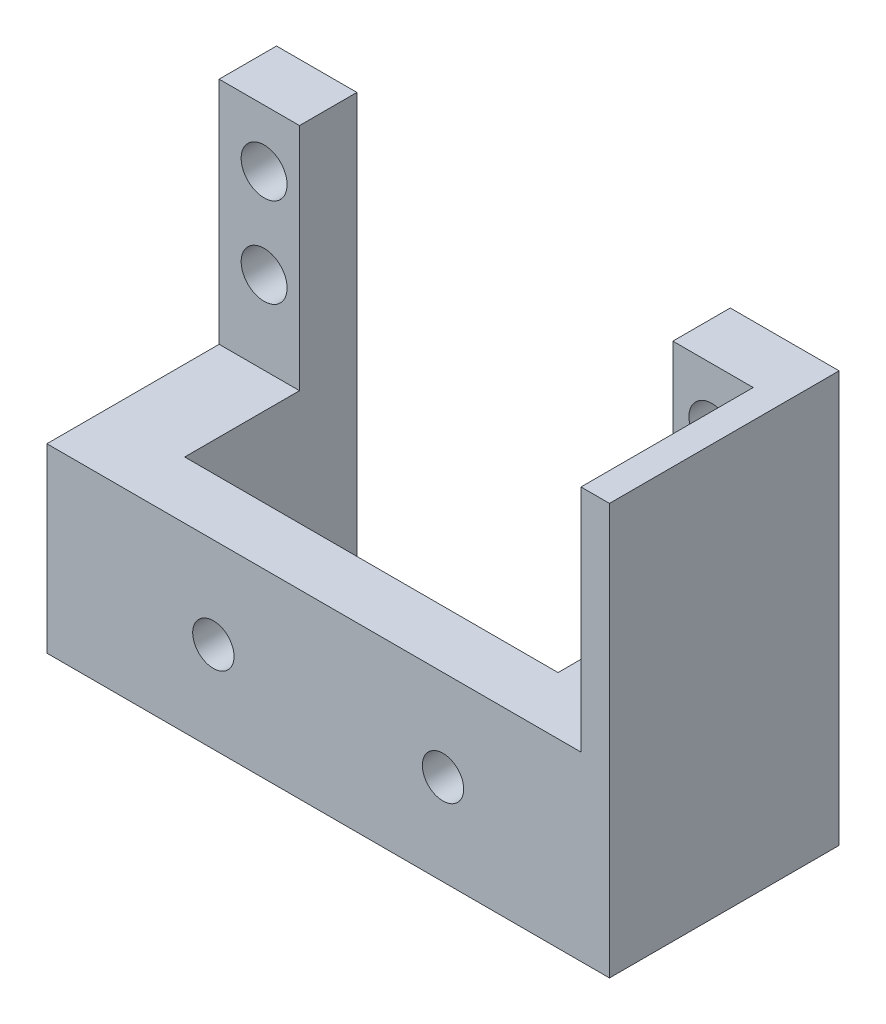
SolidWorks part; units mm, degrees
ref_plane "Front Plane" through (0, 0, 0) normal (0, 0, 1) x (1, 0, 0)
ref_plane "Top Plane" through (0, 0, 0) normal (0, 1, 0) x (1, 0, 0)
ref_plane "Right Plane" through (0, 0, 0) normal (1, 0, 0) x (0, 0, -1)
sketch "Sketch1" plane through (0, 0, 0) normal (0, 0, 1) x (1, 0, 0)
  line L17 (3781.2519, 11.566) -> (3843.4819, 11.566)
  line L18 (3781.2519, 11.566) -> (3781.2519, -8.5)
  line L19 (3781.2519, -8.5) -> (3843.4819, -8.5)
  line L20 (3843.4819, 11.566) -> (3843.4819, -8.5)
  dimension "D2" = 20.066
  dimension "D1" = 62.23
extrude "Boss-Extrude1" add sketch "Sketch1" along normal blind 25.4
sketch "Sketch3" plane through (0, 11.566, 0) normal (0, 1, 0) x (1, 0, 0)
  line L0 (3831.4423, 0) -> (3831.4423, -6.35)
  line L2 (3831.4423, -6.35) -> (3840.3323, -6.35)
  line L3 (3840.3323, -6.35) -> (3840.3323, -25.4)
  line L5 (3840.3323, -25.4) -> (3843.4819, -25.4)
  line L6 (3843.4819, -25.4) -> (3843.4819, 0)
  line L7 (3843.4819, 0) -> (3831.4423, 0)
  line L8 (3781.2519, 0) -> (3843.4819, 0) construction
  line L9 (3843.4819, -25.4) -> (3843.4819, 0) construction
  line L10 (3781.2519, -25.4) -> (3843.4819, -25.4) construction
  dimension "D1" = 3.1496
  dimension "D2" = 8.89
  dimension "D3" = 19.05
extrude "Boss-Extrude2" add sketch "Sketch3" along normal blind 25.4
sketch "Sketch4" plane through (0, 11.566, 0) normal (0, 1, 0) x (1, 0, 0)
  line L0 (3781.2519, 0) -> (3790.1419, 0)
  line L2 (3790.1419, 0) -> (3790.1419, -6.35)
  line L3 (3790.1419, -6.35) -> (3781.2519, -6.35)
  line L4 (3781.2519, -25.4) -> (3781.2519, 0) construction
  line L5 (3781.2519, -6.35) -> (3781.2519, 0)
  line L6 (3831.4423, -6.35) -> (3840.3323, -6.35) construction
  line L7 (3781.2519, 0) -> (3831.4423, 0) construction
  dimension "D1" = 8.89
extrude "Boss-Extrude3" add sketch "Sketch4" along normal up to surface (25.4 mm away) up to face at (3838.4188, 36.966, 10.5833)
sketch "Sketch5" plane through (0, 0, 6.35) normal (0, 0, 1) x (1, 0, 0)
  line L1 (3831.4423, 36.966) -> (3840.3323, 36.966) construction
  line L19 (3831.4423, 36.966) -> (3831.4423, 11.566) construction
  circle A0 centre (3835.7603, 30.616) radius 2.54
  circle A1 centre (3835.7603, 20.71) radius 2.54
  circle A2 centre (3786.2303, 20.71) radius 2.54
  circle A3 centre (3786.2303, 30.616) radius 2.54
  dimension "D1" = 4.318
  dimension "D3" = 5.08
  dimension "D2" = 6.35
  dimension "D4" = 9.906
  dimension "D5" = 49.53
extrude "Cut-Extrude1" cut sketch "Sketch5" against normal through all
sketch "Sketch10" plane through (0, 0, 0) normal (0, 0, -1) x (-1, 0, 0)
  line L0 (-3781.2519, -8.5) -> (-3843.4819, -8.5) construction
  line L1 (-3831.4423, 11.566) -> (-3790.1419, 11.566)
  line L2 (-3831.4423, 11.566) -> (-3831.4423, -8.5)
  line L3 (-3831.4423, -8.5) -> (-3790.1419, -8.5)
  line L4 (-3790.1419, 11.566) -> (-3790.1419, -8.5)
extrude "Cut-Extrude6" cut sketch "Sketch10" against normal blind 19.05
sketch "Sketch11" plane through (0, 0, 25.4) normal (0, 0, 1) x (1, 0, 0)
  line L0 (3781.2519, 1.533) -> (3843.4819, 1.533) construction
  line L1 (3781.2519, 11.566) -> (3781.2519, -8.5) construction
  line L2 (3843.4819, 36.966) -> (3843.4819, -8.5) construction
  circle A0 centre (3799.6669, 1.533) radius 2.286
  circle A1 centre (3825.0669, 1.533) radius 2.286
  point P10 (3812.3669, 1.533)
  dimension "D3" = 4.572
  dimension "D1" = 12.7
  dimension "D2" = 12.7
extrude "Cut-Extrude7" cut sketch "Sketch11" against normal through all
